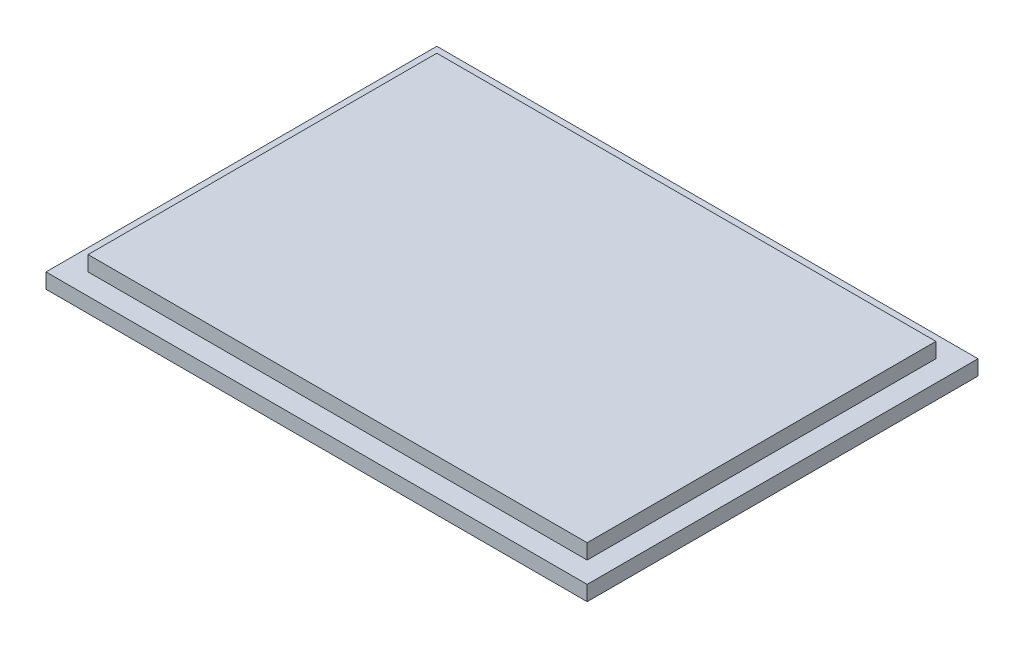
SolidWorks part; units mm, degrees
ref_plane "前视基准面" through (0, 0, 0) normal (0, 0, 1) x (1, 0, 0)
ref_plane "上视基准面" through (0, 0, 0) normal (0, 1, 0) x (1, 0, 0)
ref_plane "右视基准面" through (0, 0, 0) normal (1, 0, 0) x (0, 0, -1)
sketch "草图1" plane through (0, 0, 0) normal (0, 1, 0) x (1, 0, 0)
  line L1 (-18, 13) -> (18, 13)
  line L2 (-18, 13) -> (-18, -13)
  line L3 (-18, -13) -> (18, -13)
  line L4 (18, 13) -> (18, -13)
  line L5 (-18, 13) -> (18, -13) construction
  line L6 (-18, -13) -> (18, 13) construction
  point P0 (0, 0)
  dimension "D1" = 36
  dimension "D2" = 26
extrude "凸台-拉伸1" add sketch "草图1" against normal blind 1 contours L2 L1 L4 L3
sketch "草图3" plane through (0, 0, 0) normal (0, 1, 0) x (1, 0, 0)
  line L1 (-16.6, -11.6) -> (16.6, -11.6)
  line L2 (-16.6, -11.6) -> (-16.6, 11.6)
  line L3 (-16.6, 11.6) -> (16.6, 11.6)
  line L4 (16.6, -11.6) -> (16.6, 11.6)
  line L5 (-16.6, -11.6) -> (16.6, 11.6) construction
  line L6 (-16.6, 11.6) -> (16.6, -11.6) construction
  point P0 (0, 0)
  dimension "D1" = 33.2
  dimension "D2" = 23.2
extrude "凸台-拉伸2" add sketch "草图3" along normal blind 1 contours L2 L1 L4 L3
